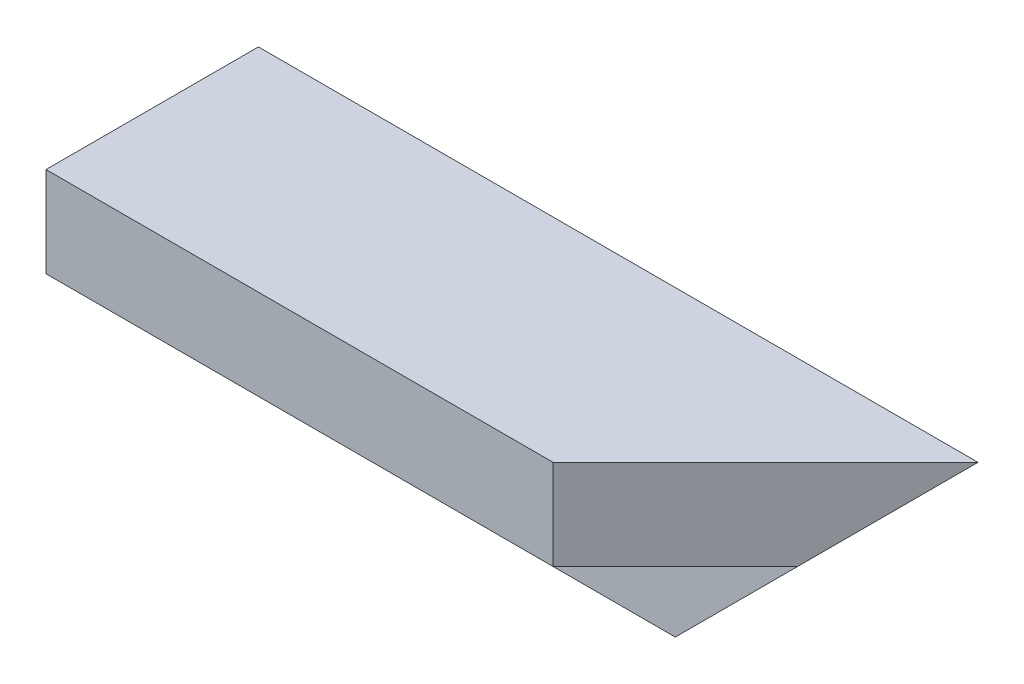
SolidWorks part; units mm, degrees
ref_plane "Plan de face" through (0, 0, 0) normal (0, 0, 1) x (1, 0, 0)
ref_plane "Plan de dessus" through (0, 0, 0) normal (0, 1, 0) x (1, 0, 0)
ref_plane "Plan de droite" through (0, 0, 0) normal (1, 0, 0) x (0, 0, -1)
sketch "Esquisse1" plane through (0, 0, 0) normal (1, 0, 0) x (0, 0, -1)
  line L0 (0, 0) -> (-40, 0)
  line L1 (-40, 0) -> (-40, -17)
  line L2 (-40, -17) -> (-17, -17)
  line L3 (-17, -17) -> (-17, -40)
  line L4 (-17, -40) -> (0, -40)
  line L5 (0, -40) -> (0, 0)
  dimension "D1" = 40
  dimension "D2" = 17
extrude "Boss.-Extru.1" add sketch "Esquisse1" along normal up to vertex (222 mm away) from vertex at 86.5
sketch "Esquisse2" plane through (0, 0, 0) normal (0, 1, 0) x (1, 0, 0)
  line L0 (222, 0) -> (182, -40)
  line L1 (222, -40) -> (86.5, -40) construction
  line L2 (182, -40) -> (222, -40)
  line L3 (222, -40) -> (222, 0)
extrude "Enlèv. mat.-Extru.1" cut sketch "Esquisse2" against normal through all
sketch "Esquisse3" plane through (0, 0, 0) normal (0, 0, -1) x (-1, 0, 0)
  line L0 (-222, 0) -> (-182, -40)
  line L1 (-222, -40) -> (-86.5, -40) construction
  line L2 (-182, -40) -> (-222, -40)
  line L3 (-222, -40) -> (-222, 0)
extrude "Enlèv. mat.-Extru.2" cut sketch "Esquisse3" against normal through all
